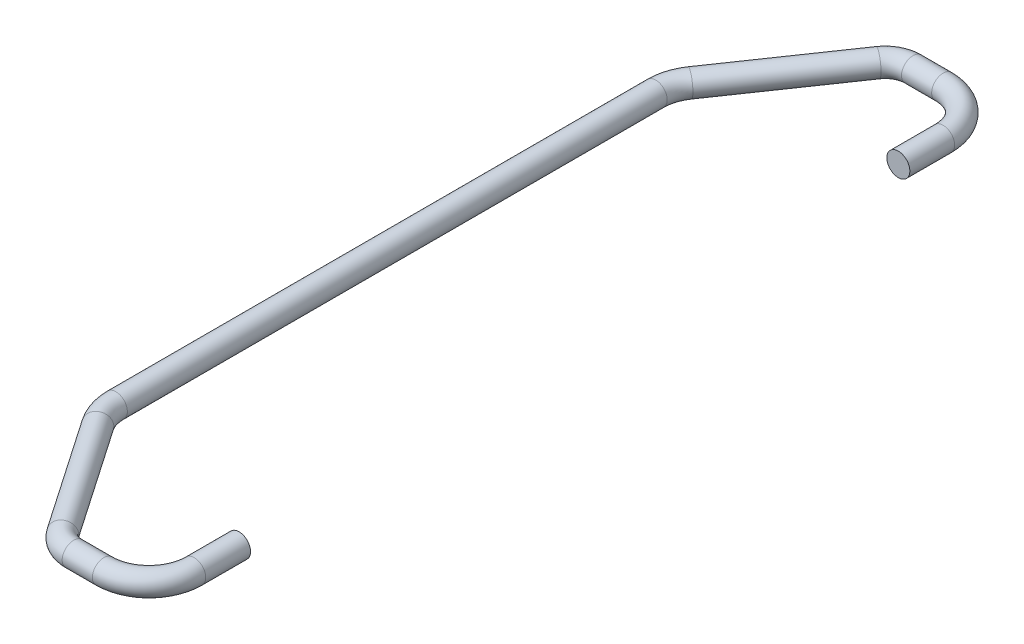
SolidWorks part; units mm, degrees
ref_plane "Front Plane" through (0, 0, 0) normal (0, 0, 1) x (1, 0, 0)
ref_plane "Top Plane" through (0, 0, 0) normal (0, 1, 0) x (1, 0, 0)
ref_plane "Right Plane" through (0, 0, 0) normal (1, 0, 0) x (0, 0, -1)
sketch "Sketch2" plane through (0, 0, 0) normal (0, 1, 0) x (1, 0, 0)
  line L0 (-42.0055, 0) -> (-42.0055, 74.5104)
  line L1 (-12.3618, 115.8059) -> (-4.0272, 115.8059)
  line L2 (8.4082, 103.3705) -> (8.4082, 90.9984)
  line L3 (-18.6451, 112.4968) -> (-39.7777, 81.6952)
  arc A1 (-4.0272, 115.8059) -> (8.4082, 103.3705) centre (-4.0272, 103.3705) cw
  arc A3 (-12.3618, 115.8059) -> (-18.6451, 112.4968) centre (-12.3618, 108.1859) ccw
  arc A4 (-42.0055, 74.5104) -> (-39.7777, 81.6952) centre (-29.3055, 74.5104) cw
  dimension "D1" = 12.7
  dimension "D2" = 7.62
sketch "Sketch3" plane through (0, 0, 0) normal (0, 0, 1) x (1, 0, 0)
  circle A0 centre (-42.0439, 0) radius 3.175
  dimension "D1" = 6.35
sweep "Sweep1" add profiles "Sketch3" path "Sketch2"
mirror "Mirror2" about plane through (-42.0439, 0, 0) normal (0, 0, 1) of "Sweep1"
